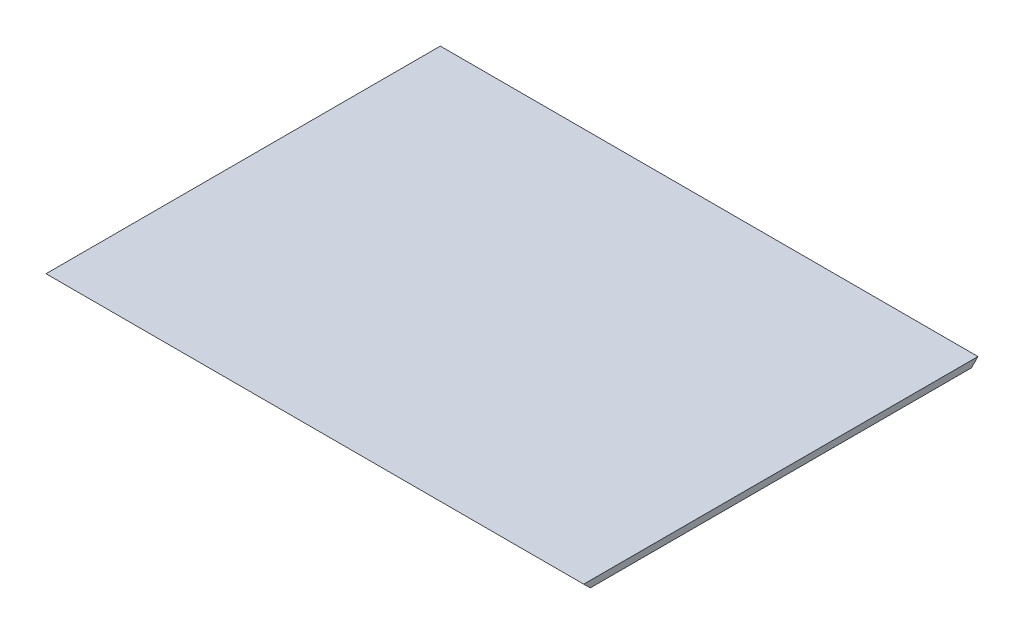
SolidWorks part; units mm, degrees
ref_plane "Front Plane" through (0, 0, 0) normal (0, 0, 1) x (1, 0, 0)
ref_plane "Top Plane" through (0, 0, 0) normal (0, 1, 0) x (1, 0, 0)
ref_plane "Right Plane" through (0, 0, 0) normal (1, 0, 0) x (0, 0, -1)
sketch "Sketch1" plane through (0, 0, 0) normal (0, 1, 0) x (1, 0, 0)
  line L1 (-130.175, -120.523) -> (130.175, -120.523)
  line L2 (-130.175, -120.523) -> (-130.175, 120.523)
  line L3 (-130.175, 120.523) -> (130.175, 120.523)
  line L4 (130.175, -120.523) -> (130.175, 120.523)
  line L5 (-130.175, -120.523) -> (130.175, 120.523) construction
  line L6 (-130.175, 120.523) -> (130.175, -120.523) construction
  point P0 (0, 0)
  dimension "D1" = 241.046
  dimension "D2" = 260.35
extrude "Boss-Extrude1" add sketch "Sketch1" along normal mid plane 3.175 contours L2 L3 L4 L1
sketch "Sketch3" plane through (-130.175, 0, 0) normal (-1, 0, 0) x (0, 0, 1)
  line L0 (120.523, 1.5875) -> (117.3168, -1.5875)
  line L2 (120.523, -1.5875) -> (-120.523, -1.5875) construction
  line L3 (117.3168, -1.5875) -> (181.7596, -66.6645)
  line L4 (181.7596, -66.6645) -> (184.9658, -63.4895)
  line L5 (-120.523, 1.5875) -> (-115.9365, -2.999)
  line L6 (-115.9365, -2.999) -> (-117.6909, -4.7534)
  line L7 (-117.6909, -4.7534) -> (-122.2774, -0.1669)
  line L8 (-122.2774, -0.1669) -> (-120.523, 1.5875)
  line L9 (184.9658, -63.4895) -> (120.523, 1.5875)
extrude "Cut-Extrude2" cut sketch "Sketch3" against normal through all
sketch "Sketch4" plane through (-130.175, 0, 0) normal (-1, 0, 0) x (0, 0, 1)
  line L0 (-95.8288, 27.0191) -> (-49.0302, -19.7795)
  line L1 (-70.3972, 1.5875) -> (-117.9283, 49.1185) construction
  line L2 (-49.0302, -19.7795) -> (-139.396, -13.402)
  line L3 (-139.396, -13.402) -> (-95.8288, 27.0191)
extrude "Cut-Extrude3" cut sketch "Sketch4" against normal through all
